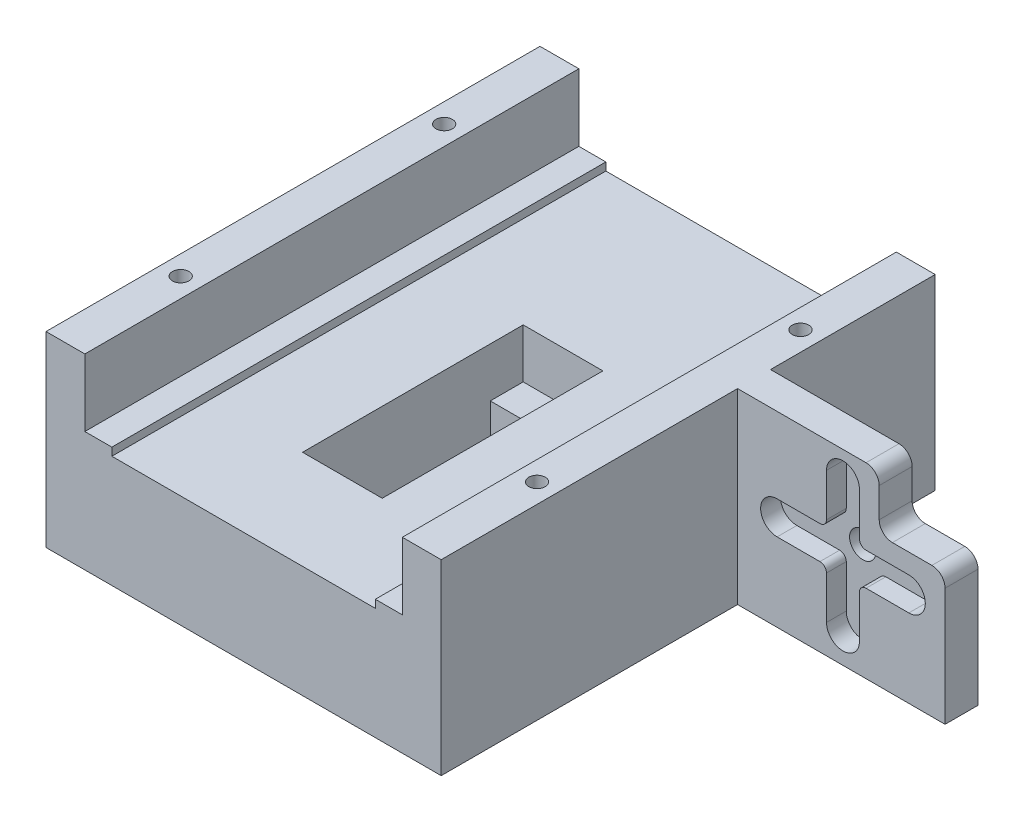
SolidWorks part; units mm, degrees
ref_plane "Ebene vorne" through (0, 0, 0) normal (0, 0, 1) x (1, 0, 0)
ref_plane "Ebene oben" through (0, 0, 0) normal (0, 1, 0) x (1, 0, 0)
ref_plane "Ebene rechts" through (0, 0, 0) normal (1, 0, 0) x (0, 0, -1)
sketch "Skizze1" plane through (0, 0, 0) normal (0, 0, 1) x (1, 0, 0)
  line L1 (0, 0) -> (-100, 0)
  line L2 (0, 0) -> (0, 50)
  line L3 (0, 50) -> (-100, 50)
  line L4 (-100, 0) -> (-100, 50)
  dimension "D1" = 100
  dimension "D2" = 50
extrude "Aufsatz-Linear austragen1" add sketch "Skizze1" along normal blind 10
sketch "Kreuz" plane through (0, 0, 10) normal (0, 0, 1) x (1, 0, 0)
  line L0 (-36.044, 25) -> (-22.5, 25) construction
  line L1 (-22.5, 42.0305) -> (-22.5, 7.9695) construction
  line L2 (-22.5, 25) -> (-14.6229, 32.8771) construction
  line L3 (-20, 42) -> (-17.727, 29.773)
  line L4 (-17.727, 29.773) -> (-5.5, 27.5)
  line L5 (-22.5, 38.1411) -> (-22.5, 25)
  line L6 (-70.944, 25) -> (25.944, 25)
  line L7 (-60.494, 25) -> (-85.1489, 25) construction
  line L8 (-25, 42) -> (-27.273, 29.773)
  line L9 (-27.273, 29.773) -> (-39.5, 27.5)
  line L10 (-20, 8) -> (-17.727, 20.227)
  line L11 (-17.727, 20.227) -> (-5.5, 22.5)
  line L12 (-27.273, 20.227) -> (-39.5, 22.5)
  line L13 (-25, 8) -> (-27.273, 20.227)
  line L14 (-2.5, 5) -> (-42.5, 5) construction
  line L15 (-2.5, 5) -> (-42.5, 45) construction
  line L16 (0, 0) -> (0, 50) construction
  arc A0 (-20, 42) -> (-25, 42) centre (-22.5, 42) ccw
  arc A1 (-5.5, 22.5) -> (-5.5, 27.5) centre (-5.5, 25) ccw
  arc A2 (-15.75, 25) -> (-22.5, 31.75) centre (-22.5, 25) ccw
  arc A4 (-39.5, 22.5) -> (-39.5, 27.5) centre (-39.5, 25) cw
  arc A5 (-20, 8) -> (-25, 8) centre (-22.5, 8) cw
  circle A6 centre (-22.5, 25) radius 5
  point P36 (0, 25)
  dimension "D1" = 5
  dimension "D2" = 5
  dimension "D3" = 13.5
  dimension "D8" = 10
  dimension "D5" = 17
  dimension "D6" = 17
  dimension "D7" = 45
  dimension "D9" = 22.5
extrude "Schnitt-Linear austragen1" [suppressed] cut sketch "Kreuz" against normal blind 8
sketch "ServoLoch" plane through (0, 0, 10) normal (0, 0, 1) x (1, 0, 0)
  circle A0 centre (-22.5, 25) radius 5
extrude "Schnitt-Linear austragen2" cut sketch "ServoLoch" against normal through all
sketch "Breite" plane through (0, 0, 10) normal (0, 0, 1) x (1, 0, 0)
  line L1 (-100, 16.5) -> (-40, 16.5)
  line L2 (-100, 16.5) -> (-100, 33.5)
  line L3 (-100, 33.5) -> (-40, 33.5)
  line L4 (-40, 16.5) -> (-40, 33.5)
  line L5 (-100, 50) -> (-100, 0) construction
  line L6 (-100, 0) -> (0, 0) construction
  dimension "D1" = 17
  dimension "D2" = 60
  dimension "D3" = 33.5
extrude "Aufsatz-Linear austragen2" add sketch "Breite" along normal blind 65
sketch "Servo" plane through (0, 33.5, 0) normal (0, 1, 0) x (1, 0, 0)
  line L4 (-63.95, -26.95) -> (-76.05, -26.95) construction
  line L5 (-76.05, -26.95) -> (-76.05, -59.55) construction
  line L10 (-76.05, -59.55) -> (-63.95, -59.55) construction
  line L11 (-100, -75) -> (-100, -10) construction
  line L12 (-63.95, -59.55) -> (-63.95, -26.95) construction
  line L13 (-63.95, -43.25) -> (-76.05, -43.25) construction
  line L15 (-63.95, -31.5) -> (-63.95, -55)
  line L16 (-63.95, -31.5) -> (-76.05, -31.5)
  line L17 (-76.05, -31.5) -> (-76.05, -55)
  line L18 (-63.95, -55) -> (-76.05, -55)
  line L21 (-40, -75) -> (-100, -75) construction
  circle A2 centre (-70, -29) radius 1
  circle A3 centre (-70, -57.5) radius 1
  circle A4 centre (-70, -37.5) radius 1.9
  point P16 (-63.95, -43.25)
  dimension "D5" = 2
  dimension "D11" = 3.8
  dimension "D13" = 6.05
  dimension "D1" = 32.6
  dimension "D2" = 12.1
  dimension "D3" = 2.05
  dimension "D4" = 6.05
  dimension "D6" = 23.5
  dimension "D7" = 23.5
  dimension "D8" = 30
  dimension "D9" = 37.5
  dimension "D10" = 8.5
  dimension "D12" = 12.1
  dimension "D14" = 2.5
  dimension "D15" = 2.5
extrude "Schnitt-Linear austragen3" cut sketch "Servo" against normal blind 60 contours L18 L15 L16 L17 A4 | A4 | A2 | A3
sketch "1,2mm Schiene" plane through (0, 33.5, 0) normal (0, 1, 0) x (1, 0, 0)
  line L12 (-40, -75) -> (-100, -75) construction
  line L13 (-100, -10) -> (-90, -10)
  line L14 (-100, -10) -> (-100, -75)
  line L15 (-100, -75) -> (-90, -75)
  line L16 (-90, -10) -> (-90, -75)
  line L18 (-40, -10) -> (-50, -10)
  line L19 (-40, -10) -> (-40, -75)
  line L20 (-40, -75) -> (-50, -75)
  line L21 (-50, -10) -> (-50, -75)
  dimension "D1" = 10
  dimension "D2" = 10
extrude "Aufsatz-Linear austragen3" add sketch "1,2mm Schiene" along normal blind 1.2
sketch "ServoTiefer legen" plane through (0, 33.5, 0) normal (0, 1, 0) x (1, 0, 0)
  line L9 (-76.05, -31.5) -> (-63.95, -31.5)
  line L10 (-76.05, -31.5) -> (-76.05, -26.5)
  line L11 (-76.05, -26.5) -> (-63.95, -26.5)
  line L12 (-63.95, -31.5) -> (-63.95, -26.5)
  line L13 (-76.05, -55) -> (-63.95, -55)
  line L14 (-76.05, -55) -> (-76.05, -60)
  line L15 (-76.05, -60) -> (-63.95, -60)
  line L16 (-63.95, -55) -> (-63.95, -60)
  dimension "D1" = 5
  dimension "D2" = 5
extrude "Schnitt-Linear austragen4" cut sketch "ServoTiefer legen" against normal blind 7.5
sketch "10,2mm Schiene" plane through (0, 34.7, 0) normal (0, 1, 0) x (1, 0, 0)
  line L0 (-100, -75) -> (-90, -75) construction
  line L1 (-94.1, -75) -> (-100, -75)
  line L2 (-94.1, -75) -> (-94.1, -10)
  line L3 (-94.1, -10) -> (-100, -10)
  line L4 (-100, -75) -> (-100, -10)
  line L6 (-40, -10) -> (-50, -10) construction
  line L7 (-40, -10) -> (-45.9, -10)
  line L8 (-40, -10) -> (-40, -75)
  line L9 (-40, -75) -> (-45.9, -75)
  line L10 (-45.9, -10) -> (-45.9, -75)
  line L11 (-50, -75) -> (-40, -75) construction
  line L12 (-100, -10) -> (-100, -75) construction
  line L13 (-40, -75) -> (-40, -10) construction
  dimension "D1" = 5.9
  dimension "D2" = 5.9
  dimension "D3" = 5.9
  dimension "D4" = 5.9
extrude "Aufsatz-Linear austragen4" add sketch "10,2mm Schiene" along normal blind 10.2
sketch "Skizze10" plane through (0, 0, 10) normal (0, 0, 1) x (1, 0, 0)
  line L0 (-100, 44.9) -> (-94.1, 44.9)
  line L1 (-94.1, 44.9) -> (-94.1, 34.7)
  line L2 (-94.1, 34.7) -> (-90, 34.7)
  line L3 (-90, 34.7) -> (-90, 33.5)
  line L4 (-90, 33.5) -> (-50, 33.5)
  line L5 (-50, 33.5) -> (-50, 34.7)
  line L6 (-50, 34.7) -> (-45.9, 34.7)
  line L7 (-45.9, 34.7) -> (-45.9, 44.9)
  line L8 (-45.9, 44.9) -> (-40, 44.9)
  line L9 (-40, 44.9) -> (-40, 52.6023)
  line L10 (-40, 52.6023) -> (-100, 52.6023)
  line L11 (-100, 52.6023) -> (-100, 44.9)
extrude "Schnitt-Linear austragen5" cut sketch "Skizze10" against normal through all
sketch "Skizze11" plane through (0, 0, 10) normal (0, 0, 1) x (1, 0, 0)
  line L0 (-40, 50) -> (0, 50)
  line L1 (0, 50) -> (0, 0)
  line L2 (0, 0) -> (-40, 0)
  line L3 (-40, 0) -> (-40, 50)
  line L4 (-45.9, 44.9) -> (-40, 44.9) construction
  circle A0 centre (-24, 30.9) radius 2
  dimension "D1" = 4
  dimension "D2" = 14
  dimension "D3" = 16
extrude "Aufsatz-Linear austragen5" add sketch "Skizze11" along normal blind 20
sketch "Skizze12" plane through (0, 0, 0) normal (0, 0, -1) x (-1, 0, 0)
  line L0 (0, 50) -> (40, 50)
  line L1 (40, 50) -> (40, 0)
  line L2 (40, 0) -> (0, 0)
  line L3 (0, 0) -> (0, 50)
extrude "Schnitt-Linear austragen6" cut sketch "Skizze12" against normal blind 25
sketch "Skizze14" plane through (0, 44.9, 0) normal (0, 1, 0) x (1, 0, 0)
  line L0 (-100, -37.5) -> (-40, -37.5) construction
  line L1 (-100, 0) -> (-100, -75) construction
  line L2 (-100, -37.5) -> (-100, -57.5) construction
  line L3 (-100, -57.5) -> (-40, -57.5) construction
  line L4 (-40, -75) -> (-40, -30) construction
  line L5 (-40, -57.5) -> (-40, -37.5) construction
  circle A0 centre (-97.05, -57.5) radius 1.25
  circle A1 centre (-42.95, -57.5) radius 1.25
  circle A2 centre (-42.95, -17.5) radius 1.25
  circle A3 centre (-97.05, -17.5) radius 1.25
  dimension "D3" = 2.5
  dimension "D5" = 2.5
  dimension "D1" = 20
  dimension "D2" = 2.95
  dimension "D4" = 2.95
sketch "Skizze15" plane through (0, 0, 30) normal (0, 0, 1) x (1, 0, 0)
  line L0 (-24, 43.4) -> (-24, 18.4) construction
  line L1 (-36.5, 30.9) -> (-11.5, 30.9) construction
  line L2 (-21.5, 40.9) -> (-21.5, 34.4)
  line L3 (-20.5, 33.4) -> (-14, 33.4)
  line L4 (-14, 28.4) -> (-20.5, 28.4)
  line L5 (-21.5, 27.4) -> (-21.5, 20.9)
  line L6 (-26.5, 20.9) -> (-26.5, 27.4)
  line L7 (-27.5, 28.4) -> (-34, 28.4)
  line L8 (-34, 33.4) -> (-27.5, 33.4)
  line L9 (-26.5, 34.4) -> (-26.5, 40.9)
  arc A0 (-21.5, 40.9) -> (-26.5, 40.9) centre (-24, 40.9) ccw
  arc A2 (-26.5, 20.9) -> (-21.5, 20.9) centre (-24, 20.9) ccw
  arc A3 (-34, 33.4) -> (-34, 28.4) centre (-34, 30.9) ccw
  arc A4 (-13.9962, 28.4) -> (-14, 33.4) centre (-14, 30.9) ccw [skipped]
  arc A5 (-14, 28.4) -> (-14, 33.4) centre (-14, 30.9) ccw
  arc A6 (-27.5, 28.4) -> (-26.5, 27.4) centre (-27.5, 27.4) cw
  arc A7 (-26.5, 34.4) -> (-27.5, 33.4) centre (-27.5, 34.4) cw
  arc A8 (-20.5, 33.4) -> (-21.5, 34.4) centre (-20.5, 34.4) cw
  arc A9 (-21.5, 27.4) -> (-20.5, 28.4) centre (-20.5, 27.4) cw
  point P16 (-24, 30.9)
  point P28 (-24, 30.9)
  point P29 (-22.499, 24.999)
  point P54 (-24, 30.9)
  dimension "D3" = 5
  dimension "D5" = 4
  dimension "D2" = 5
  dimension "D8" = 1
  dimension "D1" = 25
  dimension "D6" = 1
  dimension "D7" = 1
  dimension "D4" = 4
extrude "Schnitt-Linear austragen8" cut sketch "Skizze15" against normal blind 3
sketch "Skizze18" plane through (0, 0, 30) normal (0, 0, 1) x (1, 0, 0)
  line L1 (0, 0) -> (-100, 0)
  line L3 (-8.5, 16.5) -> (-100, 16.5)
  line L4 (-100, 0) -> (-100, 16.5)
  line L8 (-8.5, 16.5) -> (-8.5, 36.4)
  line L9 (-40, 50) -> (0, 50)
  line L11 (-18.5, 44.9) -> (-18.5, 36.4)
  line L12 (-18.5, 36.4) -> (-8.5, 36.4)
  line L15 (-40, 50) -> (-40, 44.9)
  line L16 (-40, 44.9) -> (-18.5, 44.9)
  line L18 (0, 50) -> (0, 0)
  line L19 (-21.5, 34.4) -> (-21.5, 40.9) construction
  line L20 (-14, 33.4) -> (-20.5, 33.4) construction
  arc A2 (-14, 28.4) -> (-14, 33.4) centre (-14, 30.9) ccw construction
  point P22 (-11.5, 30.9)
  dimension "D1" = 3
  dimension "D2" = 3
  dimension "D3" = 3
extrude "Schnitt-Linear austragen9" cut sketch "Skizze18" against normal blind 30 and the other way through all
fillet "Verrundung5" radius 2 1 edges at (-18.5, 44.9, 27.5)
fillet "Verrundung6" radius 2 1 edges at (-18.5, 36.4, 27.5)
fillet "Verrundung7" radius 2 1 edges at (-8.5, 36.4, 27.5)
extrude "Schnitt-Linear austragen10" cut sketch "Skizze14" against normal blind 5
